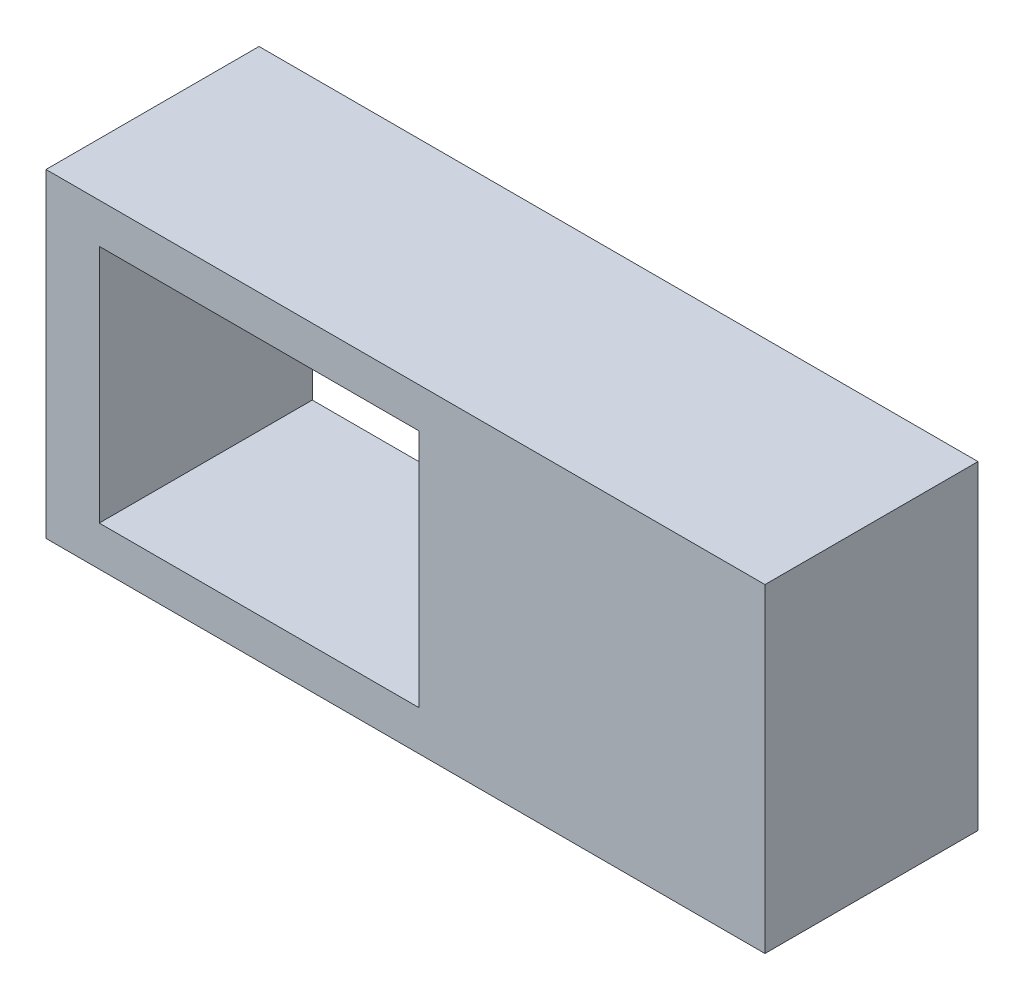
SolidWorks part; units mm, degrees
ref_plane "前视基准面" through (0, 0, 0) normal (0, 0, 1) x (1, 0, 0)
ref_plane "上视基准面" through (0, 0, 0) normal (0, 1, 0) x (1, 0, 0)
ref_plane "右视基准面" through (0, 0, 0) normal (1, 0, 0) x (0, 0, -1)
sketch "草图1" plane through (0, 0, 0) normal (0, 0, 1) x (1, 0, 0)
  line L1 (-13.5, 6) -> (13.5, 6)
  line L2 (-13.5, 6) -> (-13.5, -6)
  line L3 (-13.5, -6) -> (13.5, -6)
  line L4 (13.5, 6) -> (13.5, -6)
  line L5 (-13.5, 6) -> (13.5, -6) construction
  line L6 (-13.5, -6) -> (13.5, 6) construction
  line L7 (-11.5, 4.5) -> (11.5, 4.5)
  line L8 (-11.5, 4.5) -> (-11.5, -4.5)
  line L9 (-11.5, -4.5) -> (11.5, -4.5)
  line L10 (11.5, 4.5) -> (11.5, -4.5)
  line L11 (-11.5, 4.5) -> (11.5, -4.5) construction
  line L12 (-11.5, -4.5) -> (11.5, 4.5) construction
  point P0 (0, 0)
  point P6 (0, 0)
  dimension "D1" = 2
  dimension "D2" = 1.5
  dimension "D3" = 23
  dimension "D4" = 9
  dimension "D5" = 2
extrude "凸台-拉伸1" add sketch "草图1" along normal blind 8
sketch "草图2" plane through (0, 0, 8) normal (0, 0, 1) x (1, 0, 0)
  line L0 (-11.5, -4.5) -> (11.5, -4.5) construction
  line L1 (11.5, 4.5) -> (0.5, 4.5)
  line L2 (11.5, 4.5) -> (11.5, -4.5)
  line L3 (11.5, -4.5) -> (0.5, -4.5)
  line L4 (0.5, 4.5) -> (0.5, -4.5)
  line L5 (-11.5, 4.5) -> (-11.5, -4.5) construction
  dimension "D1" = 12
extrude "凸台-拉伸2" add sketch "草图2" against normal blind 2
sketch "草图3" plane through (0, 0, 6) normal (0, 0, -1) x (-1, 0, 0)
  line L0 (-11.5, -4.5) -> (-11.5, 4.5) construction
  circle A0 centre (-6.35, 0) radius 1.55
  circle A1 centre (-6.35, 0) radius 2.75
  dimension "D2" = 3.1
  dimension "D3" = 5.5
  dimension "D1" = 5.15
extrude "凸台-拉伸3" add sketch "草图3" along normal blind 5
sketch "草图5" plane through (-11.5, 0, 0) normal (1, 0, 0) x (0, 0, -1)
  line L0 (0, -6) -> (0, 6) construction
  line L1 (-4.5943, 3.5) -> (-2.5943, 3.5)
  line L2 (-4.5943, 3.5) -> (-4.5943, -3.5)
  line L3 (-4.5943, -3.5) -> (-2.5943, -3.5)
  line L4 (-2.5943, 3.5) -> (-2.5943, -3.5)
  dimension "D1" = 7
  dimension "D2" = 2
  dimension "D3" = 3.5
  dimension "3.9" = 2.5943
sketch "草图6" plane through (11.5, 0, 0) normal (-1, 0, 0) x (0, 0, 1)
  line L0 (0, 6) -> (0, -6) construction
  line L1 (3.9, 3.5) -> (5.9, 3.5)
  line L2 (3.9, 3.5) -> (3.9, -3.5)
  line L3 (3.9, -3.5) -> (5.9, -3.5)
  line L4 (5.9, 3.5) -> (5.9, -3.5)
  dimension "D1" = 7
  dimension "D2" = 2
  dimension "D3" = 3.9
  dimension "D4" = 3.5
